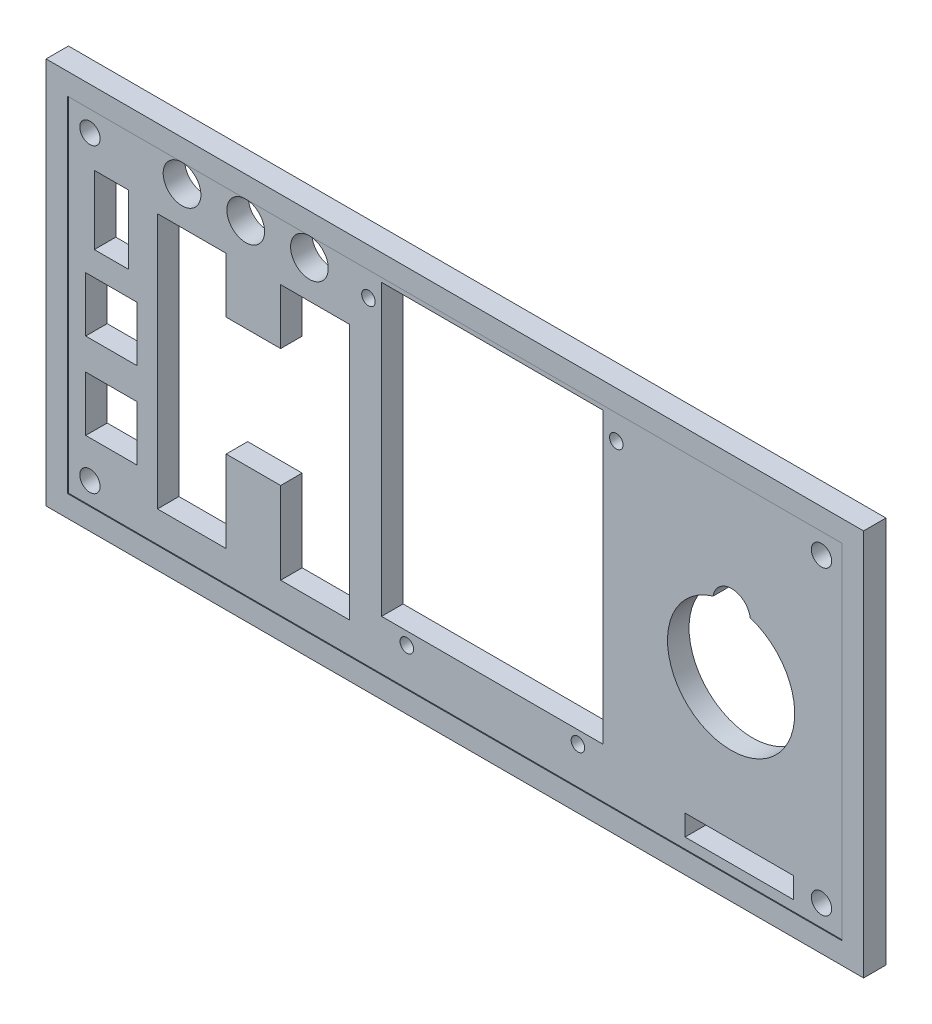
SolidWorks part; units mm, degrees
ref_plane "Front Plane" through (0, 0, 0) normal (0, 0, 1) x (1, 0, 0)
ref_plane "Top Plane" through (0, 0, 0) normal (0, 1, 0) x (1, 0, 0)
ref_plane "Right Plane" through (0, 0, 0) normal (1, 0, 0) x (0, 0, -1)
sketch "Model" plane through (0, 0, 0) normal (0, 0, 1) x (1, 0, 0)
  line L0 (0, 0) -> (114.2864, 0)
  line L1 (114.2864, 0) -> (114.2864, 50.7864)
  line L2 (114.2864, 50.7864) -> (0, 50.7864)
  line L3 (0, 50.7864) -> (0, 0)
  line L4 (13.1379, 4.5435) -> (23.2721, 4.5435)
  line L5 (23.2721, 4.5435) -> (23.2721, 42.2805)
  line L6 (23.2721, 42.2805) -> (13.1379, 42.2805)
  line L7 (13.1379, 42.2805) -> (13.1379, 4.5435)
  line L8 (31.315, 4.5225) -> (41.4492, 4.5225)
  line L9 (41.4492, 4.5225) -> (41.4492, 42.3015)
  line L10 (41.4492, 42.3015) -> (31.315, 42.3015)
  line L11 (31.315, 42.3015) -> (31.315, 4.5225)
  line L12 (46.2086, 7.3498) -> (78.8994, 7.3498)
  line L13 (78.8994, 7.3498) -> (78.8994, 50.0406)
  line L14 (78.8994, 50.0406) -> (46.2086, 50.0406)
  line L15 (46.2086, 50.0406) -> (46.2086, 7.3498)
  line L16 (3.8168, 33.0268) -> (8.8696, 33.0268)
  line L17 (8.8696, 33.0268) -> (8.8696, 43.1596)
  line L18 (8.8696, 43.1596) -> (3.8168, 43.1596)
  line L19 (3.8168, 43.1596) -> (3.8168, 33.0268)
  line L20 (2.5466, 21.3426) -> (10.1398, 21.3426)
  line L21 (10.1398, 21.3426) -> (10.1398, 29.4438)
  line L22 (10.1398, 29.4438) -> (2.5466, 29.4438)
  line L23 (2.5466, 29.4438) -> (2.5466, 21.3426)
  line L24 (2.5466, 8.6426) -> (10.1398, 8.6426)
  line L25 (10.1398, 8.6426) -> (10.1398, 16.7438)
  line L26 (10.1398, 16.7438) -> (2.5466, 16.7438)
  line L27 (2.5466, 16.7438) -> (2.5466, 8.6426)
  line L28 (23.2721, 16.6293) -> (31.315, 16.6293)
  line L30 (31.315, 34.1205) -> (23.2721, 34.1205)
  line L32 (90.991, 1.5367) -> (106.9676, 1.5367)
  line L33 (106.9676, 1.5367) -> (106.9676, 4.6101)
  line L34 (106.9676, 4.6101) -> (90.991, 4.6101)
  line L35 (90.991, 4.6101) -> (90.991, 1.5367)
  circle A0 centre (111.125, 47.625) radius 1.5
  circle A1 centre (3.175, 47.625) radius 1.5
  circle A2 centre (3.175, 3.175) radius 1.5
  circle A3 centre (111.125, 3.175) radius 1.5
  circle A4 centre (44.2722, 47.0662) radius 1
  circle A5 centre (49.9364, 5.5118) radius 1
  circle A6 centre (75.184, 5.5118) radius 1
  circle A7 centre (80.8482, 47.0662) radius 1
  circle A8 centre (97.79, 25.4) radius 9.3853
  circle A9 centre (97.8662, 33.9598) radius 2.7686
  circle A10 centre (16.764, 47.879) radius 2.7813
  circle A11 centre (26.162, 47.879) radius 2.7813
  circle A12 centre (35.56, 47.879) radius 2.7813
ref_plane "Plane1" through (0, 0, 0) normal (0, 0, 1) x (1, 0, 0)
sketch "Sketch1" plane through (0, 0, 0) normal (0, 0, 1) x (1, 0, 0)
  line L0 (57.1432, 50.7864) -> (57.1432, 0) construction
  line L1 (-3.175, -3.175) -> (117.4614, -3.175)
  line L2 (-3.175, -3.175) -> (-3.175, 53.9614)
  line L3 (-3.175, 53.9614) -> (117.4614, 53.9614)
  line L4 (117.4614, -3.175) -> (117.4614, 53.9614)
  line L5 (-3.175, -3.175) -> (117.4614, 53.9614) construction
  line L6 (-3.175, 53.9614) -> (117.4614, -3.175) construction
  line L7 (114.2864, 50.7864) -> (0, 50.7864) construction
  line L8 (0, 0) -> (114.2864, 0) construction
  line L9 (0, 50.7864) -> (114.2864, 50.7864) construction
  line L10 (114.2864, 50.7864) -> (114.2864, 0) construction
  line L12 (0, 0) -> (114.2864, 0)
  line L13 (0, 0) -> (0, 50.7864)
  line L14 (0, 50.7864) -> (114.2864, 50.7864)
  line L15 (114.2864, 0) -> (114.2864, 50.7864)
  line L16 (0, 0) -> (114.2864, 50.7864) construction
  line L17 (0, 50.7864) -> (114.2864, 0) construction
  point P0 (57.1432, 25.3932)
  point P11 (57.1432, 25.3932)
  dimension "D1" = 3.175
  dimension "D2" = 3.175
extrude "Boss-Extrude1" add sketch "Model" along normal blind 3.175 contours L2 L3 L0 L1 A12 A11 A10 A9 A8 A7 A6 A5 A4 A3 A2 A1 A0 L35 L34 L33 L32 L30 L11 L10 L9 L8 L28 L5 L4 L7 L6 L27 L26 L25
extrude "Boss-Extrude2" add sketch "Sketch1" along normal blind 3.302 contours L1 L4 L3 L2 L15 L12 L13 L14
